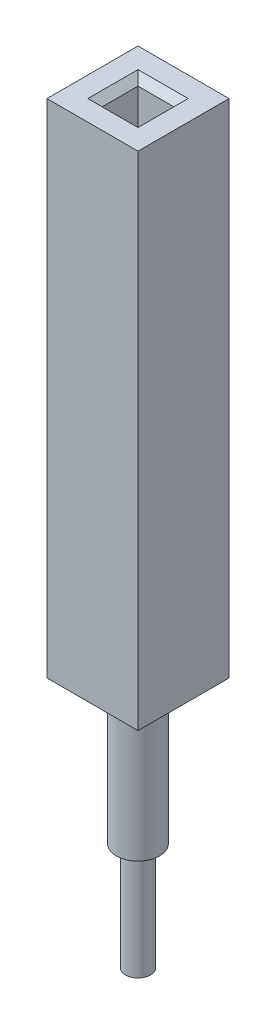
SolidWorks part; units mm, degrees
ref_plane "Спереди" through (0, 0, 0) normal (0, 0, 1) x (1, 0, 0)
ref_plane "Сверху" through (0, 0, 0) normal (0, 1, 0) x (1, 0, 0)
ref_plane "Справа" through (0, 0, 0) normal (1, 0, 0) x (0, 0, -1)
sketch "Эскиз1" plane through (0, 0, 0) normal (0, 1, 0) x (1, 0, 0)
  line L1 (-1.27, 1.27) -> (1.27, 1.27)
  line L2 (-1.27, 1.27) -> (-1.27, -1.27)
  line L3 (-1.27, -1.27) -> (1.27, -1.27)
  line L4 (1.27, 1.27) -> (1.27, -1.27)
  line L5 (-1.27, 1.27) -> (1.27, -1.27) construction
  line L6 (-1.27, -1.27) -> (1.27, 1.27) construction
  line L7 (-0.5, 0.5) -> (0.5, 0.5)
  line L8 (-0.5, 0.5) -> (-0.5, -0.5)
  line L9 (-0.5, -0.5) -> (0.5, -0.5)
  line L10 (0.5, 0.5) -> (0.5, -0.5)
  line L11 (-0.5, 0.5) -> (0.5, -0.5) construction
  line L12 (-0.5, -0.5) -> (0.5, 0.5) construction
  point P0 (0, 0)
  point P6 (0, 0)
  dimension "D1" = 2.54
  dimension "D2" = 1
extrude "Бобышка-Вытянуть1" add sketch "Эскиз1" along normal blind 14
chamfer "Фаска1" distance 0.2 angle 45 4 edges at (0, 14, 0.5) (0.5, 14, 0) (0, 14, -0.5) (-0.5, 14, 0)
ref_plane "Плоскость1" through (0, 3, 0) normal (0, -1, 0) x (-1, 0, 0)
sketch "Эскиз3" plane through (0, 3, 0) normal (0, -1, 0) x (-1, 0, 0)
  circle A0 centre (0, 0) radius 0.6
  dimension "D1" = 1.2
extrude "Бобышка-Вытянуть2" add sketch "Эскиз3" along normal blind 7 separate body
sketch "Эскиз4" plane through (0, -4, 0) normal (0, -1, 0) x (1, 0, 0)
  circle A0 centre (0, 0) radius 0.35
  dimension "D1" = 0.7
extrude "Бобышка-Вытянуть3" add sketch "Эскиз4" along normal blind 3 separate body
